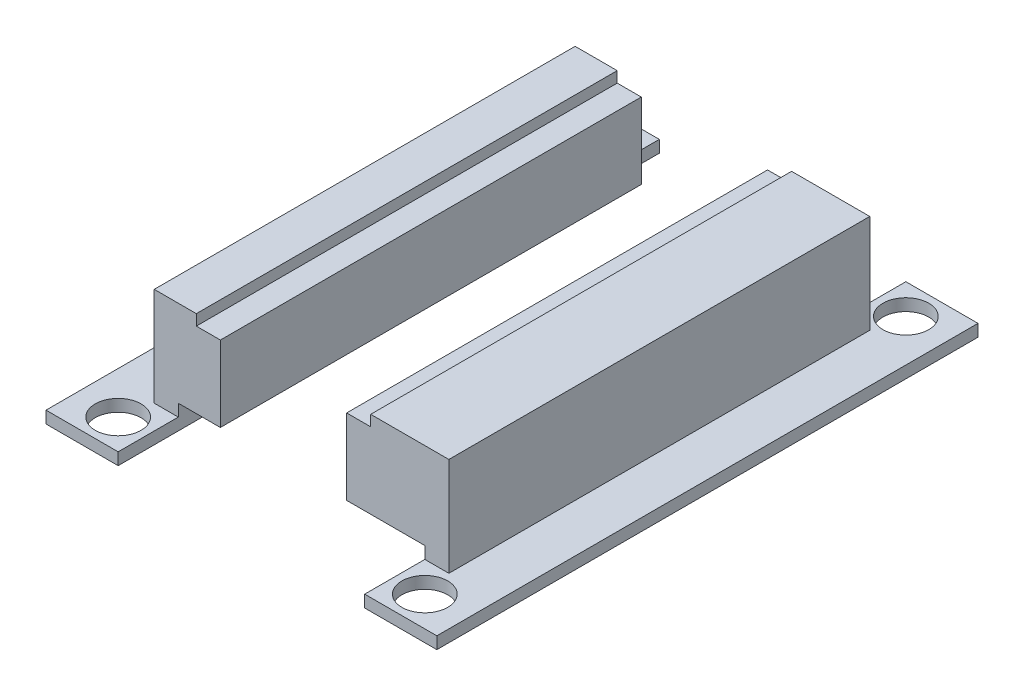
SolidWorks part; units mm, degrees
ref_plane "Front Plane" through (0, 0, 0) normal (0, 0, 1) x (1, 0, 0)
ref_plane "Top Plane" through (0, 0, 0) normal (0, 1, 0) x (1, 0, 0)
ref_plane "Right Plane" through (0, 0, 0) normal (1, 0, 0) x (0, 0, -1)
sketch "Sketch1" plane through (0, 0, 0) normal (0, 1, 0) x (1, 0, 0)
  line L0 (-10.25, 0) -> (10.25, 0)
  dimension "D1" = 20.5
sketch "Sketch2" plane through (0, 0, 0) normal (0, 0, 1) x (1, 0, 0)
  line L11 (-10.25, 0) -> (10.25, 0) construction
  line L16 (0, -0.5712) -> (0, 1.3971) construction
  line L33 (10.25, 0) -> (10.25, 2)
  line L34 (10.25, 2) -> (3.75, 2)
  line L35 (3.75, 2) -> (3.75, 8.3)
  line L36 (3.75, 8.3) -> (5.75, 8.3)
  line L37 (5.75, 8.3) -> (5.75, 9.2)
  line L38 (-6.75, 8.3) -> (-6.75, 2)
  line L39 (-6.75, 2) -> (-10.25, 2)
  line L40 (-6.75, 8.3) -> (-8.75, 8.3)
  line L41 (-8.75, 8.3) -> (-8.75, 9.2)
  line L42 (-8.75, 9.2) -> (-12.25, 9.2)
  line L43 (-10.25, 2) -> (-10.25, 0)
  line L44 (-16.25, 0) -> (-10.25, 0)
  line L45 (5.75, 9.2) -> (12.25, 9.2)
  line L46 (12.25, 9.2) -> (12.25, 1)
  line L47 (-12.25, 9.2) -> (-12.25, 1)
  line L48 (-12.25, 1) -> (-16.25, 1)
  line L49 (-16.25, 1) -> (-16.25, 0)
  line L50 (12.25, 1) -> (16.25, 1)
  line L51 (16.25, 1) -> (16.25, 0)
  line L52 (16.25, 0) -> (10.25, 0)
  point P14 (-16.25, 0.5)
  point P24 (-8.75, 8.75)
  point P25 (0, 0)
  point P34 (16.25, 0.5)
  dimension "D2" = 0.9
  dimension "D3" = 8.3
  dimension "D4" = 1
  dimension "D5" = 4
  dimension "D6" = 3.5
  dimension "D7" = 2
  dimension "D8" = 8.3
  dimension "D9" = 1
  dimension "D10" = 2
  dimension "D11" = 2
  dimension "D12" = 2
  dimension "D13" = 6.5
  dimension "D14" = 0.9
  dimension "D15" = 2
  dimension "D16" = 2
  dimension "D17" = 4
extrude "Boss-Extrude3" add sketch "Sketch2" along normal blind 45
sketch "Sketch4" plane through (12.25, 0, 0) normal (1, 0, 0) x (0, 0, -1)
  line L0 (-45, 1) -> (-40, 1)
  line L1 (-40, 1) -> (-40, 9.2)
  line L2 (-40, 9.2) -> (-45, 9.2)
  line L3 (-45, 9.2) -> (-45, 1)
  line L4 (-45, 1) -> (0, 1) construction
  line L5 (-45, 9.2) -> (0, 9.2) construction
  line L7 (-45, 1) -> (-45, 9.2) construction
  dimension "D1" = 5
extrude "Cut-Extrude1" cut sketch "Sketch4" against normal through all
sketch "Sketch5" plane through (0, 1, 0) normal (0, 1, 0) x (1, 0, 0)
  line L0 (-10.25, -45) -> (-16.25, -45) construction
  line L1 (-10.25, -40) -> (-10.25, -45) construction
  line L2 (16.25, -45) -> (16.25, 0) construction
  line L3 (16.25, -45) -> (10.25, -45) construction
  circle A0 centre (-12.75, -42.5) radius 1.905
  circle A1 centre (12.75, -42.5) radius 1.905
  dimension "D1" = 3.81
  dimension "D2" = 3.81
  dimension "D3" = 2.5
  dimension "D4" = 2.5
  dimension "D5" = 3.5
  dimension "D6" = 2.5
extrude "Cut-Extrude2" cut sketch "Sketch5" against normal through all
sketch "Sketch6" plane through (12.25, 0, 0) normal (1, 0, 0) x (0, 0, -1)
  line L0 (0, 1) -> (0, 9.2) construction
  line L1 (-5, 1) -> (0, 1)
  line L2 (-5, 1) -> (-5, 9.2)
  line L3 (-5, 9.2) -> (0, 9.2)
  line L4 (0, 1) -> (0, 9.2)
  line L5 (-5, 1) -> (0, 9.2) construction
  line L6 (-5, 9.2) -> (0, 1) construction
  line L7 (-40, 9.2) -> (0, 9.2) construction
  line L8 (-45, 1) -> (0, 1) construction
  point P0 (-2.5, 5.1)
  dimension "D1" = 5
extrude "Cut-Extrude3" cut sketch "Sketch6" against normal through all
sketch "Sketch7" plane through (0, 1, 0) normal (0, 1, 0) x (1, 0, 0)
  line L0 (-10.25, 0) -> (-10.25, -5) construction
  line L1 (10.25, -5) -> (10.25, 0) construction
  line L2 (-10.25, 0) -> (-16.25, 0) construction
  line L3 (16.25, 0) -> (10.25, 0) construction
  circle A0 centre (-12.75, -2.5) radius 1.905
  circle A1 centre (12.75, -2.5) radius 1.905
  point P4 (0, 0)
  point P5 (-20.4774, -4.6147)
  point P6 (-12.7999, -2.7697)
  point P7 (13.0896, -2.7697)
  dimension "D1" = 3.81
  dimension "D2" = 3.81
  dimension "D3" = 2.5
  dimension "D4" = 2.5
  dimension "D5" = 2.5
  dimension "D6" = 2.5
extrude "Cut-Extrude4" cut sketch "Sketch7" against normal through all
